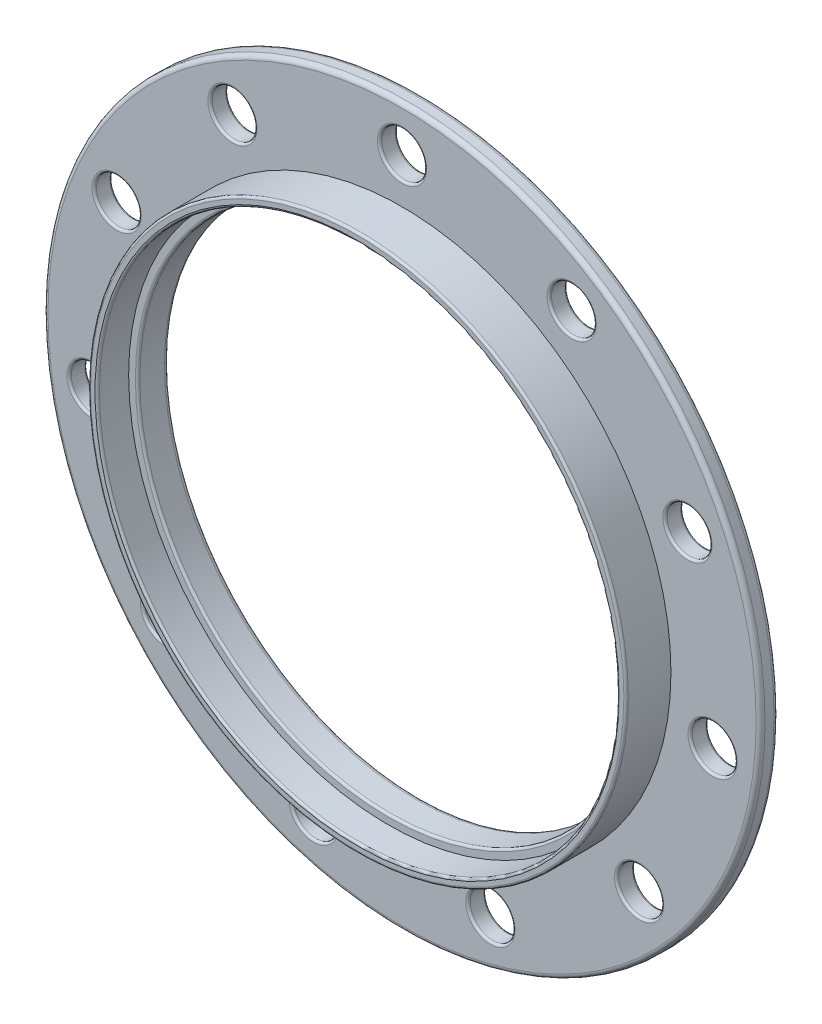
SolidWorks part; units mm, degrees
material "PET"
ref_plane "Front Plane" through (0, 0, 0) normal (0, 0, 1) x (1, 0, 0)
ref_plane "Top Plane" through (0, 0, 0) normal (0, 1, 0) x (1, 0, 0)
ref_plane "Right Plane" through (0, 0, 0) normal (1, 0, 0) x (0, 0, -1)
sketch "Sketch1" plane through (0, 0, 0) normal (0, 0, 1) x (1, 0, 0)
  circle A0 centre (0, 0) radius 40
  dimension "D1" = 80
extrude "Boss-Extrude1" add sketch "Sketch1" along normal blind 2
sketch "Sketch2" plane through (0, 0, 2) normal (0, 0, 1) x (1, 0, 0)
  circle A0 centre (0, 0) radius 30
  circle A1 centre (0, 0) radius 29
  dimension "D1" = 60
  dimension "D2" = 58
extrude "Boss-Extrude2" add sketch "Sketch2" along normal blind 5
sketch "Sketch3" plane through (0, 0, 2) normal (0, 0, 1) x (1, 0, 0)
  circle A0 centre (0, 0) radius 29 construction
  circle A1 centre (0, 0) radius 29
extrude "Cut-Extrude1" cut sketch "Sketch3" against normal through all
sketch "Sketch4" plane through (0, 0, 2) normal (0, 0, 1) x (1, 0, 0)
  circle A0 centre (0, 0) radius 35 construction
  circle A1 centre (0, 35) radius 2.5
  circle A2 centre (18.9224, 29.4439) radius 2.5
  circle A3 centre (31.8371, 14.5395) radius 2.5
  circle A4 centre (34.6438, -4.981) radius 2.5
  circle A5 centre (26.4512, -22.9201) radius 2.5
  circle A6 centre (9.8606, -33.5823) radius 2.5
  circle A7 centre (-9.8606, -33.5823) radius 2.5
  circle A8 centre (-26.4512, -22.9201) radius 2.5
  circle A9 centre (-34.6438, -4.981) radius 2.5
  circle A10 centre (-31.8371, 14.5395) radius 2.5
  circle A11 centre (-18.9224, 29.4439) radius 2.5
  point P28 (0, 0)
  dimension "D1" = 70
  dimension "D2" = 5
  dimension "D3" = 11
extrude "Cut-Extrude2" cut sketch "Sketch4" against normal through all
sketch "Sketch5" plane through (0, 0, 0) normal (0, 0, -1) x (-1, 0, 0)
  circle A0 centre (0, 0) radius 29
  circle A1 centre (0, 0) radius 28
  circle A2 centre (0, 0) radius 29 construction
  dimension "D1" = 1
extrude "Boss-Extrude3" add sketch "Sketch5" against normal blind 3.5
fillet "Fillet1" radius 0.25 3 edges at (29, 0, 7) (30, 0, 7) (-28, 0, 3.5)
fillet "Fillet2" radius 0.5 3 edges at (-28, 0, 0) (40, 0, 0) (40, 0, 2)
fillet "Fillet3" radius 0.25 22 edges at (28.9512, -22.9201, 0) (28.9512, -22.9201, 2) (37.1438, -4.981, 0) (37.1438, -4.981, 2) (34.3371, 14.5395, 0) (34.3371, 14.5395, 2) (21.4224, 29.4439, 0) (21.4224, 29.4439, 2) (2.5, 35, 0) (2.5, 35, 2) (-16.4224, 29.4439, 2) (-16.4224, 29.4439, 0) (-29.3371, 14.5395, 2) (-29.3371, 14.5395, 0) (-32.1438, -4.981, 2) (-32.1438, -4.981, 0) (-23.9512, -22.9201, 2) (-23.9512, -22.9201, 0) (-7.3606, -33.5823, 2) (-7.3606, -33.5823, 0) (12.3606, -33.5823, 2) (12.3606, -33.5823, 0)
